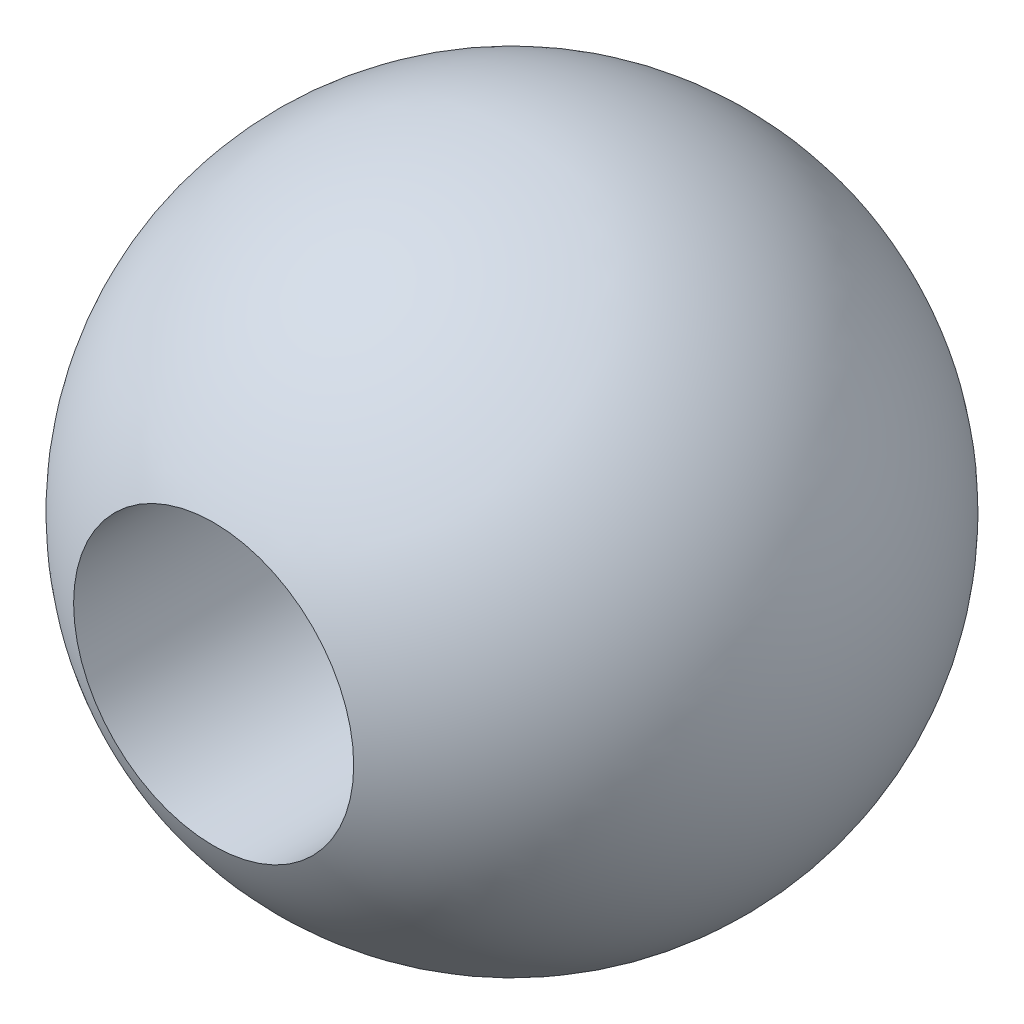
SolidWorks part; units mm, degrees
ref_plane "Front" through (0, 0, 0) normal (0, 0, 1) x (1, 0, 0)
ref_plane "Top" through (0, 0, 0) normal (0, 1, 0) x (1, 0, 0)
ref_plane "Right" through (0, 0, 0) normal (1, 0, 0) x (0, 0, -1)
sketch "草图2" plane through (0, 0, 0) normal (0, 1, 0) x (1, 0, 0)
  line L0 (-34.5193, 0) -> (-30.5193, 0)
  arc A0 (-30.5193, 0) -> (-34.5193, 0) centre (-32.5193, 0) ccw
revolve "旋转1" add sketch "草图2" angle 360 about L0
sketch "草图4" plane through (0, 0, 0) normal (0, 0, 1) x (1, 0, 0)
  circle A0 centre (-32.5193, 0) radius 2
  circle A1 centre (-32.5193, 0) radius 0.85
  dimension "D1" = 1.7
extrude "切除-拉伸2" cut sketch "草图4" against normal through all and the other way through all contours A1
sketch "草图5" plane through (0, 0, 0) normal (0, 0, 1) x (1, 0, 0)
  circle A0 centre (-32.5193, 0) radius 2
